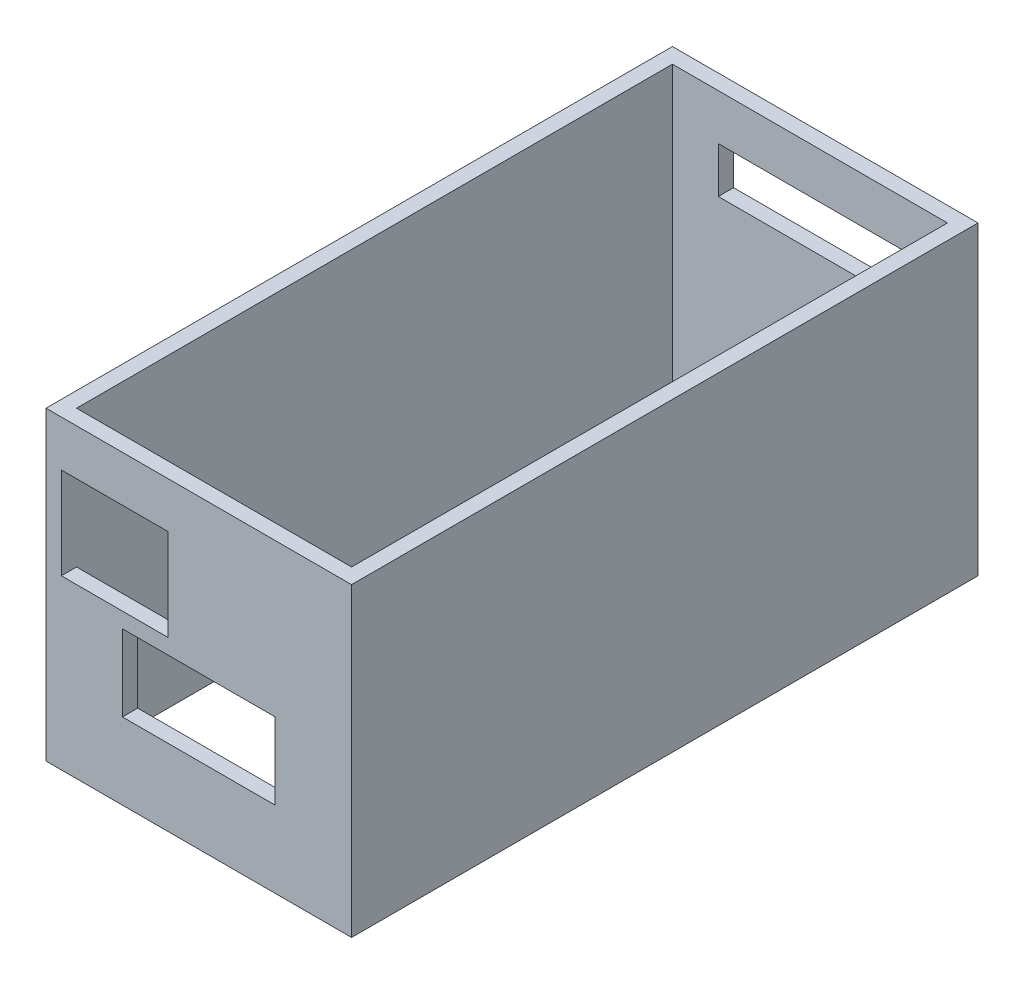
SolidWorks part; units mm, degrees
ref_plane "Front Plane" through (0, 0, 0) normal (0, 0, 1) x (1, 0, 0)
ref_plane "Top Plane" through (0, 0, 0) normal (0, 1, 0) x (1, 0, 0)
ref_plane "Right Plane" through (0, 0, 0) normal (1, 0, 0) x (0, 0, -1)
sketch "Sketch1" plane through (0, 0, 0) normal (0, 1, 0) x (1, 0, 0)
  line L0 (-2, 80) -> (38, 80)
  line L1 (0, 0) -> (36, 0)
  line L2 (0, 0) -> (0, 78)
  line L3 (0, 78) -> (36, 78)
  line L4 (36, 0) -> (36, 78)
  line L5 (38, -2) -> (38, 80)
  line L6 (-2, -2) -> (38, -2)
  line L7 (-2, -2) -> (-2, 80)
  dimension "D1" = 36
  dimension "D2" = 78
  dimension "D3" = 2
extrude "Boss-Extrude1" add sketch "Sketch1" along normal blind 40
sketch "Sketch2" plane through (0, 0, 2) normal (0, 0, 1) x (1, 0, 0)
  line L0 (-2, 40) -> (-2, 0) construction
  line L1 (8, 20) -> (28, 20)
  line L2 (8, 20) -> (8, 10)
  line L3 (8, 10) -> (28, 10)
  line L4 (28, 20) -> (28, 10)
  line L5 (0, 34) -> (14, 34)
  line L6 (0, 34) -> (0, 22)
  line L7 (0, 22) -> (14, 22)
  line L8 (14, 34) -> (14, 22)
  line L9 (-2, 40) -> (38, 40) construction
  line L10 (-2, 0) -> (38, 0) construction
  point P4 (11.553, 5.9682)
  dimension "D1" = 12
  dimension "D2" = 14
  dimension "D3" = 6
  dimension "D4" = 2
  dimension "D5" = 20
  dimension "D6" = 10
  dimension "D7" = 10
  dimension "D8" = 8
extrude "Cut-Extrude1" cut sketch "Sketch2" against normal blind 20
sketch "Sketch3" plane through (0, 0, -80) normal (0, 0, -1) x (-1, 0, 0)
  line L0 (-38, 40) -> (-38, 0) construction
  line L1 (-30, 34) -> (-6, 34)
  line L2 (-30, 34) -> (-30, 28)
  line L3 (-30, 28) -> (-6, 28)
  line L4 (-6, 34) -> (-6, 28)
  line L5 (2, 40) -> (2, 0) construction
  line L6 (-38, 40) -> (2, 40) construction
  dimension "D1" = 8
  dimension "D2" = 8
  dimension "D3" = 6
  dimension "D4" = 6
sketch "Sketch4" plane through (0, 0, -80) normal (0, 0, -1) x (-1, 0, 0)
  line L0 (-38, 40) -> (2, 40) construction
  line L1 (-36, 38) -> (0, 38)
  line L2 (-36, 38) -> (-36, 2)
  line L3 (-36, 2) -> (0, 2)
  line L4 (0, 38) -> (0, 2)
  line L5 (-38, 40) -> (-38, 0) construction
  line L6 (-38, 0) -> (2, 0) construction
  line L7 (2, 40) -> (2, 0) construction
  line L9 (-34, 36) -> (-2, 36)
  line L10 (-2, 36) -> (-2, 4)
  line L11 (-34, 4) -> (-2, 4)
  line L12 (-34, 36) -> (-34, 4)
  dimension "D1" = 2
  dimension "D2" = 2
  dimension "D3" = 2
  dimension "D4" = 2
  dimension "D5" = 2
extrude "Boss-Extrude2" add sketch "Sketch4" along normal blind 2
extrude "Cut-Extrude2" cut sketch "Sketch3" against normal blind 2
